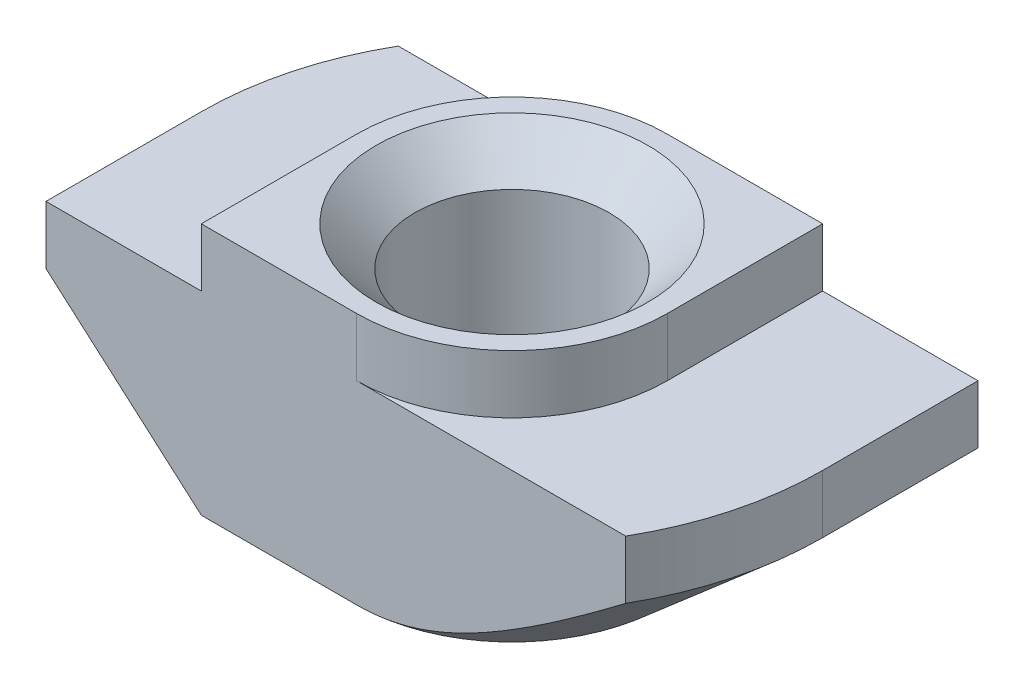
SolidWorks part; units mm, degrees
material "Сталь 20  ГОСТ 1050-2013"
ref_plane "Спереди" through (0, 0, 0) normal (0, 0, 1) x (1, 0, 0)
ref_plane "Сверху" through (0, 0, 0) normal (0, 1, 0) x (1, 0, 0)
ref_plane "Справа" through (0, 0, 0) normal (1, 0, 0) x (0, 0, -1)
sketch "Эскиз1" plane through (0, 0, 0) normal (0, 0, 1) x (1, 0, 0)
  line L0 (4, 0) -> (-4, 0)
  line L1 (-4, 0) -> (-4, -1.5)
  line L2 (-4, -1.5) -> (-8, -1.5)
  line L3 (-8, -1.5) -> (-8, -6.5)
  line L4 (-8, -6.5) -> (8, -6.5)
  line L5 (0, -6.5) -> (0, 0) construction
  line L6 (8, -1.5) -> (8, -6.5)
  line L7 (4, -1.5) -> (8, -1.5)
  line L8 (4, 0) -> (4, -1.5)
  dimension "D1" = 8
  dimension "D2" = 16
  dimension "D3" = 6.5
  dimension "D4" = 1.5
extrude "Бобышка-Вытянуть1" add sketch "Эскиз1" along normal mid plane 8
hole_wizard "Отверстие обработанное метчиком M61" positions "Эскиз2" profile "Эскиз3" tap size "M6" standard "ISO" end condition up to next
sketch "Эскиз2" plane through (0, 0, 0) normal (0, 1, 0) x (1, 0, 0)
  point P0 (0, 0)
sketch "Эскиз3" plane through (0, 0, 0) normal (1, 0, 0) x (0, 0, 1)
  line L0 (0, 0) -> (0, 6.5)
  line L1 (0, 6.5) -> (3.5, 6.5)
  line L2 (2.5, 5.5) -> (2.5, 1)
  line L3 (2.5, 1) -> (3.5, 0)
  line L5 (3.5, 0) -> (0, 0)
  line L6 (-2.5, 1) -> (-3.5, 0) construction
  line L7 (3.5, 6.5) -> (2.5, 5.5)
  line L8 (-3.5, 6.5) -> (-2.5, 5.5) construction
  line L11 (0, -6.35) -> (0, 107.95) construction
  dimension "Диаметр проходного сверла" = 5
  dimension "Глубина проходного сверла" = 6.5
  dimension "Диаметр передней зенковки" = 7
  dimension "Угол передней зенковки" = 90
  dimension "Диаметр задней зенковки" = 7
  dimension "Угол задней зенковки" = 90
cosmetic thread "Отверстие резьбы1" parameters "D2"=6
sketch "Эскиз4" plane through (0, 0, 0) normal (0, 1, 0) x (1, 0, 0)
  line L0 (-4, 4) -> (-4, 0)
  line L1 (-4, -4) -> (-4, 4) construction
  line L2 (4, 4) -> (-4, 4) construction
  line L3 (0, 4) -> (-4, 4)
  line L4 (0, -4) -> (4, -4)
  line L5 (4, -4) -> (-4, -4) construction
  line L6 (4, -4) -> (4, 0)
  line L7 (4, -4) -> (4, 4) construction
  arc A0 (-4, 0) -> (0, 4) centre (0, 0) cw
  arc A1 (4, 0) -> (0, -4) centre (0, 0) cw
extrude "Вырез-Вытянуть1" cut sketch "Эскиз4" against normal up to surface (1.5 mm away) up to face at (-6, -1.5, 0)
sketch "Эскиз5" plane through (0, -1.5, 0) normal (0, 1, 0) x (1, 0, 0)
  line L0 (-8, 0) -> (-8, 4)
  line L1 (-8, -4) -> (-8, 4) construction
  line L2 (-8, 4) -> (-6.9282, 4)
  line L3 (0, 4) -> (-8, 4) construction
  line L4 (8, 0) -> (8, -4)
  line L5 (8, -4) -> (8, 4) construction
  line L6 (8, -4) -> (6.9282, -4)
  line L7 (8, -4) -> (0, -4) construction
  arc A0 (-6.9282, 4) -> (-8, 0) centre (0, 0) ccw
  arc A2 (8, 0) -> (6.9282, -4) centre (0, 0) cw
  point P19 (0, 0)
extrude "Вырез-Вытянуть2" cut sketch "Эскиз5" against normal through all
sketch "Эскиз6" plane through (0, 0, 4) normal (0, 0, 1) x (1, 0, 0)
  line L0 (-8, -3) -> (-8, -6.5)
  line L1 (-8, -1.5) -> (-8, -6.5) construction
  line L2 (-8, -6.5) -> (-4, -6.5)
  line L3 (-8, -6.5) -> (6.9282, -6.5) construction
  line L4 (-4, -6.5) -> (-8, -3)
  line L5 (-4, -1.5) -> (-8, -1.5) construction
  line L6 (-4, 0) -> (-4, -1.5) construction
  point P10 (0, 0)
  dimension "D1" = 1.5
sketch "Эскиз7" plane through (0, -6.5, 0) normal (0, -1, 0) x (1, 0, 0)
  line L0 (0, 8) -> (-8, 8)
  line L1 (-8, 8) -> (-8, 0)
  line L2 (0, -8) -> (8, -8)
  line L3 (8, -8) -> (8, 0)
  arc A0 (-8, 0) -> (0, -8) centre (0, 0) ccw
  arc A1 (8, 0) -> (0, 8) centre (0, 0) ccw
sweep "Вырез-По траектории1" cut profiles "Эскиз6" path "Эскиз7"
